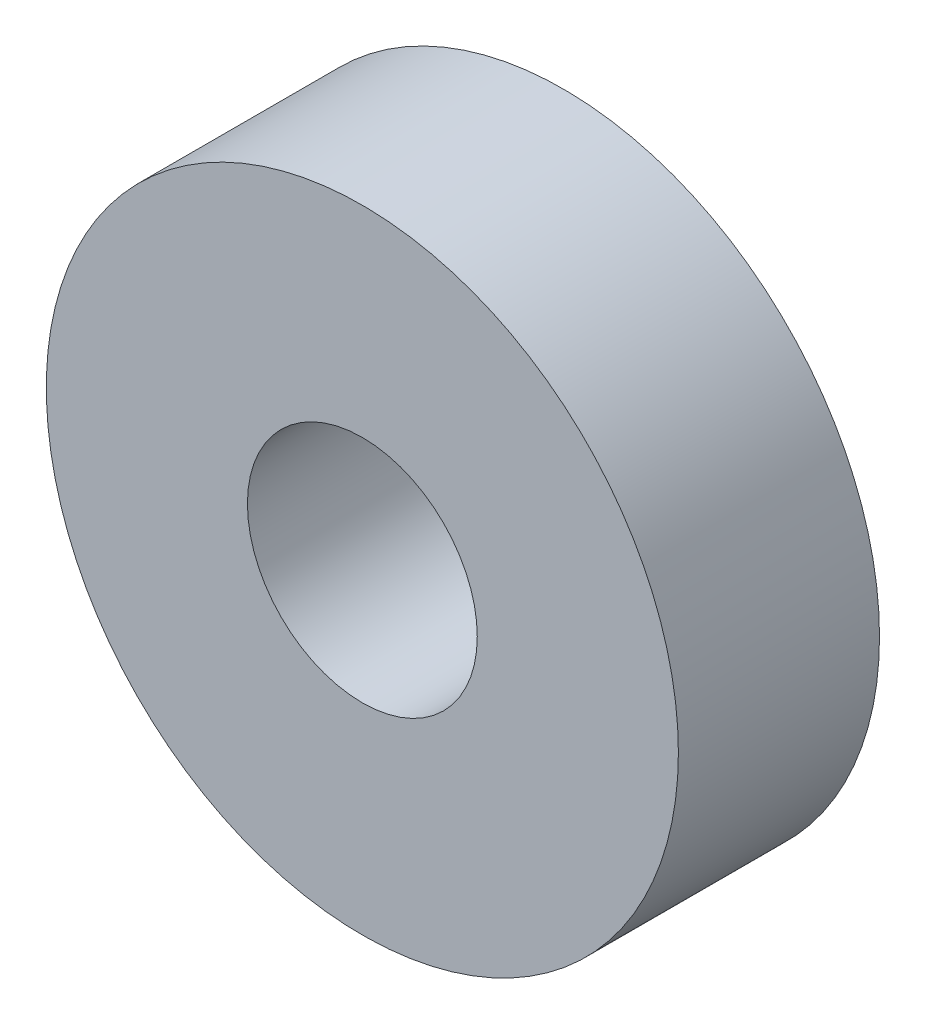
SolidWorks part; units mm, degrees
ref_plane "Alzado" through (0, 0, 0) normal (0, 0, 1) x (1, 0, 0)
ref_plane "Planta" through (0, 0, 0) normal (0, 1, 0) x (1, 0, 0)
ref_plane "Vista lateral" through (0, 0, 0) normal (1, 0, 0) x (0, 0, -1)
sketch "Croquis1" plane through (0, 0, 0) normal (0, 0, 1) x (1, 0, 0)
  circle A0 centre (0, 0) radius 11
  circle A1 centre (0, 0) radius 4
  dimension "D1" = 22
  dimension "D2" = 8
extrude "Saliente-Extruir1" add sketch "Croquis1" along normal blind 7
